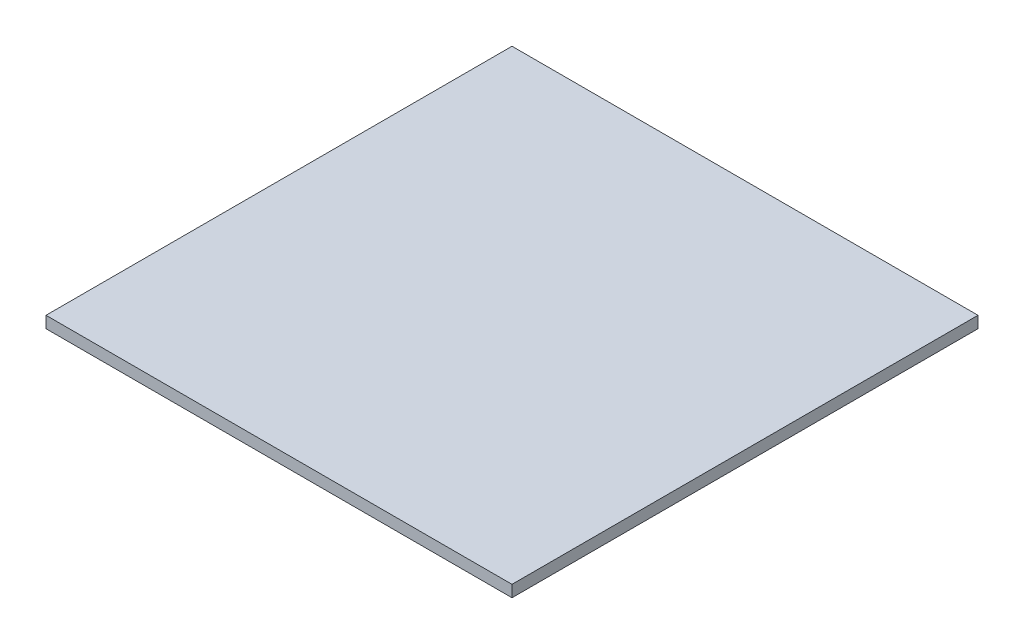
SolidWorks part; units mm, degrees
ref_plane "Face" through (0, 0, 0) normal (0, 0, 1) x (1, 0, 0)
ref_plane "Dessus" through (0, 0, 0) normal (0, 1, 0) x (1, 0, 0)
ref_plane "Droite" through (0, 0, 0) normal (1, 0, 0) x (0, 0, -1)
sketch "Esquisse1" plane through (0, 0, 0) normal (0, 1, 0) x (1, 0, 0)
  line L1 (0, 0) -> (400, 0)
  line L2 (0, 0) -> (0, 400)
  line L3 (0, 400) -> (400, 400)
  line L4 (400, 0) -> (400, 400)
  dimension "D1" = 400
  dimension "D2" = 400
extrude "Extrusion1" add sketch "Esquisse1" along normal blind 10
